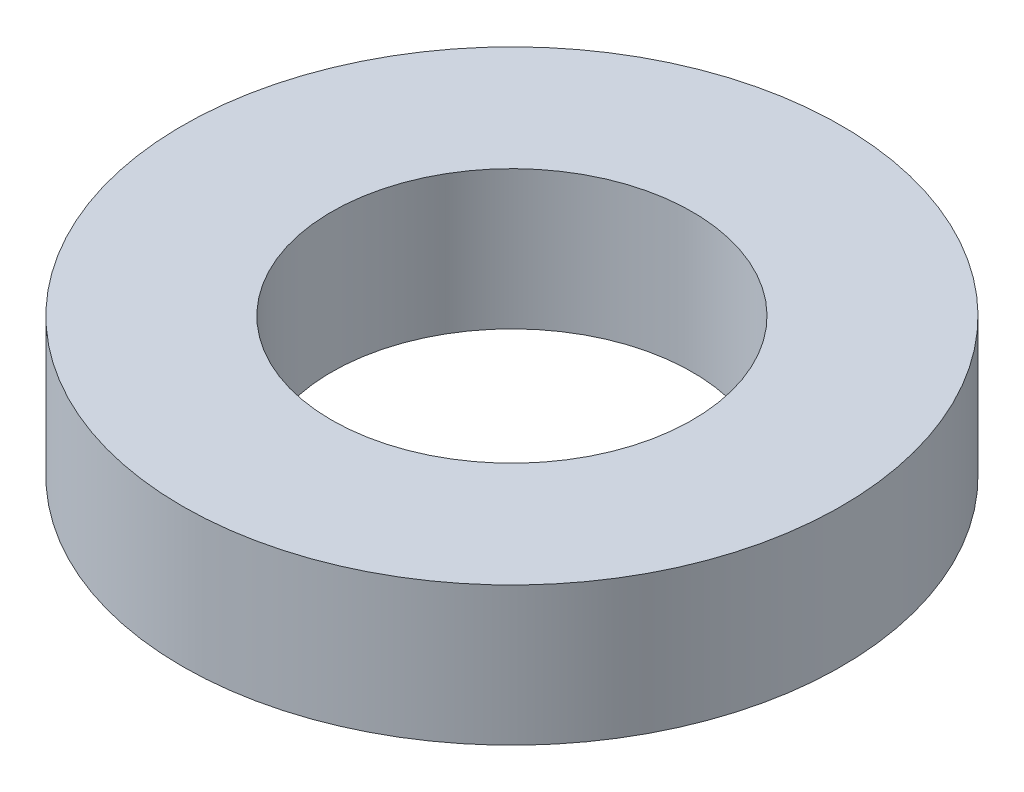
SolidWorks part; units mm, degrees
ref_plane "Front Plane" through (0, 0, 0) normal (0, 0, 1) x (1, 0, 0)
ref_plane "Top Plane" through (0, 0, 0) normal (0, 1, 0) x (1, 0, 0)
ref_plane "Right Plane" through (0, 0, 0) normal (1, 0, 0) x (0, 0, -1)
sketch "Sketch1" plane through (0, 0, 0) normal (0, 1, 0) x (1, 0, 0)
  circle A0 centre (0, 0) radius 4.75
  circle A1 centre (0, 0) radius 2.6
  dimension "D1" = 5.2
  dimension "D2" = 9.5
extrude "Boss-Extrude1" add sketch "Sketch1" along normal blind 2
